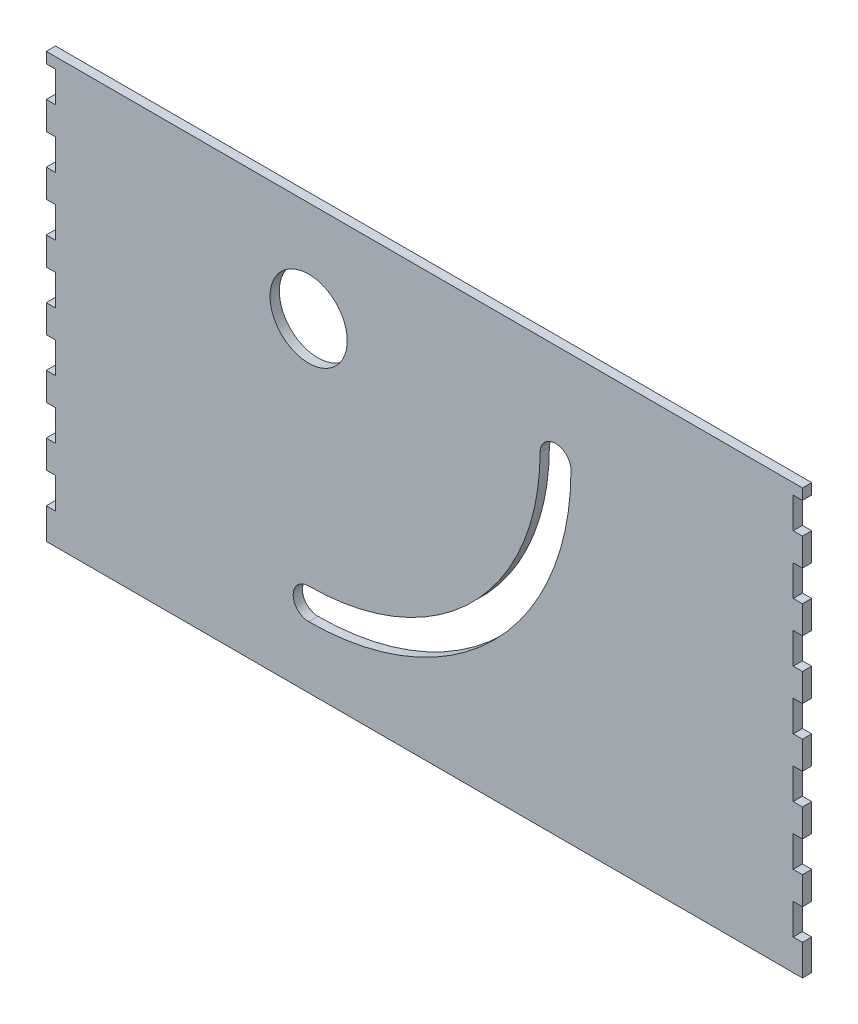
SolidWorks part; units mm, degrees
material "birch 3mm plywood"
ref_plane "Front Plane" through (0, 0, 0) normal (0, 0, 1) x (1, 0, 0)
ref_plane "Top Plane" through (0, 0, 0) normal (0, 1, 0) x (1, 0, 0)
ref_plane "Right Plane" through (0, 0, 0) normal (1, 0, 0) x (0, 0, -1)
sketch "Sketch1" plane through (0, 0, 0) normal (0, 0, 1) x (1, 0, 0)
  line L0 (244.5, 137.5) -> (244.5, 134)
  line L1 (-0.5, 137.5) -> (244.5, 137.5)
  line L2 (-0.5, 137.5) -> (-0.5, 0) construction
  line L3 (-0.5, 0) -> (244.5, 0)
  line L4 (244.5, 137.5) -> (244.5, 0) construction
  line L5 (84.5, 59.75) -> (84.5, -77.75) construction
  line L6 (244.5, 134) -> (241.5, 134)
  line L7 (241.5, 134) -> (241.5, 124)
  line L8 (241.5, 124) -> (244.5, 124)
  line L9 (244.5, 124) -> (244.5, 115)
  line L10 (244.5, 105) -> (244.5, 96)
  line L11 (241.5, 115) -> (241.5, 105)
  line L12 (241.5, 105) -> (244.5, 105)
  line L13 (244.5, 115) -> (241.5, 115)
  line L14 (244.5, 86) -> (244.5, 77)
  line L15 (241.5, 96) -> (241.5, 86)
  line L16 (241.5, 86) -> (244.5, 86)
  line L17 (244.5, 96) -> (241.5, 96)
  line L18 (244.5, 67) -> (244.5, 58)
  line L19 (241.5, 77) -> (241.5, 67)
  line L20 (241.5, 67) -> (244.5, 67)
  line L21 (244.5, 77) -> (241.5, 77)
  line L22 (244.5, 48) -> (244.5, 39)
  line L23 (241.5, 58) -> (241.5, 48)
  line L24 (241.5, 48) -> (244.5, 48)
  line L25 (244.5, 58) -> (241.5, 58)
  line L26 (244.5, 29) -> (244.5, 20)
  line L27 (241.5, 39) -> (241.5, 29)
  line L28 (241.5, 29) -> (244.5, 29)
  line L29 (244.5, 39) -> (241.5, 39)
  line L30 (244.5, 10) -> (244.5, 0)
  line L31 (241.5, 20) -> (241.5, 10)
  line L32 (241.5, 10) -> (244.5, 10)
  line L33 (244.5, 20) -> (241.5, 20)
  line L34 (122, 137.5) -> (122, 0) construction
  line L35 (-0.5, 10) -> (-0.5, 0)
  line L36 (-0.5, 20) -> (2.5, 20)
  line L37 (2.5, 10) -> (-0.5, 10)
  line L38 (2.5, 20) -> (2.5, 10)
  line L39 (-0.5, 39) -> (2.5, 39)
  line L40 (2.5, 29) -> (-0.5, 29)
  line L41 (2.5, 39) -> (2.5, 29)
  line L42 (-0.5, 29) -> (-0.5, 20)
  line L43 (-0.5, 58) -> (2.5, 58)
  line L44 (2.5, 48) -> (-0.5, 48)
  line L45 (2.5, 58) -> (2.5, 48)
  line L46 (-0.5, 48) -> (-0.5, 39)
  line L47 (-0.5, 77) -> (2.5, 77)
  line L48 (2.5, 67) -> (-0.5, 67)
  line L49 (2.5, 77) -> (2.5, 67)
  line L50 (-0.5, 67) -> (-0.5, 58)
  line L51 (-0.5, 96) -> (2.5, 96)
  line L52 (2.5, 86) -> (-0.5, 86)
  line L53 (2.5, 96) -> (2.5, 86)
  line L54 (-0.5, 86) -> (-0.5, 77)
  line L55 (-0.5, 115) -> (2.5, 115)
  line L56 (2.5, 105) -> (-0.5, 105)
  line L57 (2.5, 115) -> (2.5, 105)
  line L58 (-0.5, 105) -> (-0.5, 96)
  line L59 (-0.5, 124) -> (-0.5, 115)
  line L60 (2.5, 124) -> (-0.5, 124)
  line L61 (2.5, 134) -> (2.5, 124)
  line L62 (-0.5, 134) -> (2.5, 134)
  line L63 (-0.5, 137.5) -> (-0.5, 134)
  arc A3 (169.5, 105) -> (159.5, 105) centre (164.5, 105) ccw
  arc A4 (159.5, 105) -> (84.5, 30) centre (84.5, 105) cw
  arc A5 (169.5, 105) -> (84.5, 20) centre (84.5, 105) cw
  arc A6 (84.5, 20) -> (84.5, 30) centre (84.5, 25) cw
  circle A7 centre (84.5, 105) radius 12.5
  dimension "D1" = 10
  dimension "D2" = 75
  dimension "D3" = 20
  dimension "D7" = 25
  dimension "D4" = 20
  dimension "D5" = 85
  dimension "D6" = 160
  dimension "D8" = 3.5
  dimension "D9" = 10
  dimension "D10" = 9
  dimension "D12" = 3
  dimension "D11" = 7
extrude "Boss-Extrude1" add sketch "Sketch1" along normal blind 3
